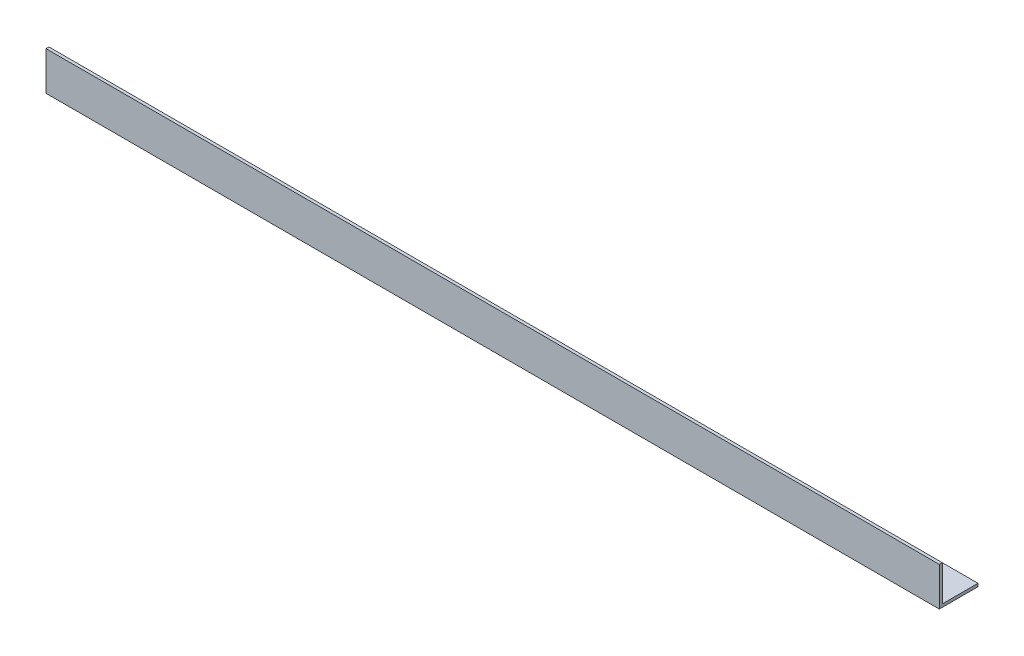
SolidWorks part; units mm, degrees
ref_plane "Спереди" through (0, 0, 0) normal (0, 0, 1) x (1, 0, 0)
ref_plane "Сверху" through (0, 0, 0) normal (0, 1, 0) x (1, 0, 0)
ref_plane "Справа" through (0, 0, 0) normal (1, 0, 0) x (0, 0, -1)
sketch "Эскиз1" plane through (0, 0, 0) normal (1, 0, 0) x (0, 0, -1)
  line L0 (0, 0) -> (0, 65)
  line L1 (0, 0) -> (65, 0)
extrude "Вытянуть-Тонкостенный1" add sketch "Эскиз1" along normal blind 1500 thin
